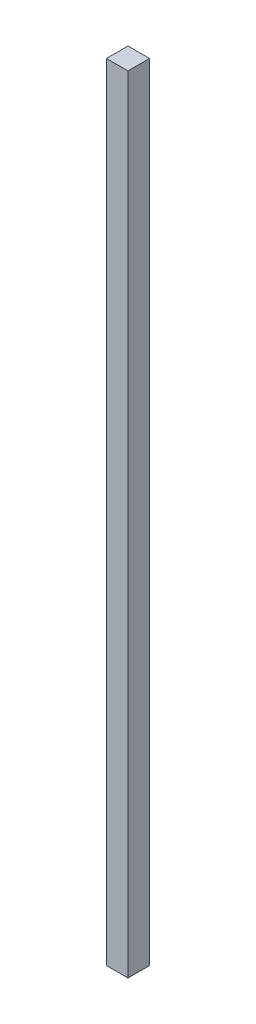
SolidWorks part; units mm, degrees
ref_plane "Front Plane" through (0, 0, 0) normal (0, 0, 1) x (1, 0, 0)
ref_plane "Top Plane" through (0, 0, 0) normal (0, 1, 0) x (1, 0, 0)
ref_plane "Right Plane" through (0, 0, 0) normal (1, 0, 0) x (0, 0, -1)
sketch "Sketch1" plane through (0, 0, 0) normal (0, 1, 0) x (1, 0, 0)
  line L1 (-38.1, 38.1) -> (38.1, 38.1)
  line L2 (-38.1, 38.1) -> (-38.1, -38.1)
  line L3 (-38.1, -38.1) -> (38.1, -38.1)
  line L4 (38.1, 38.1) -> (38.1, -38.1)
  line L5 (-38.1, 38.1) -> (38.1, -38.1) construction
  line L6 (-38.1, -38.1) -> (38.1, 38.1) construction
  point P0 (0, 0)
  dimension "D1" = 76.2
  dimension "D2" = 76.2
extrude "Boss-Extrude1" add sketch "Sketch1" along normal blind 2775.0687
